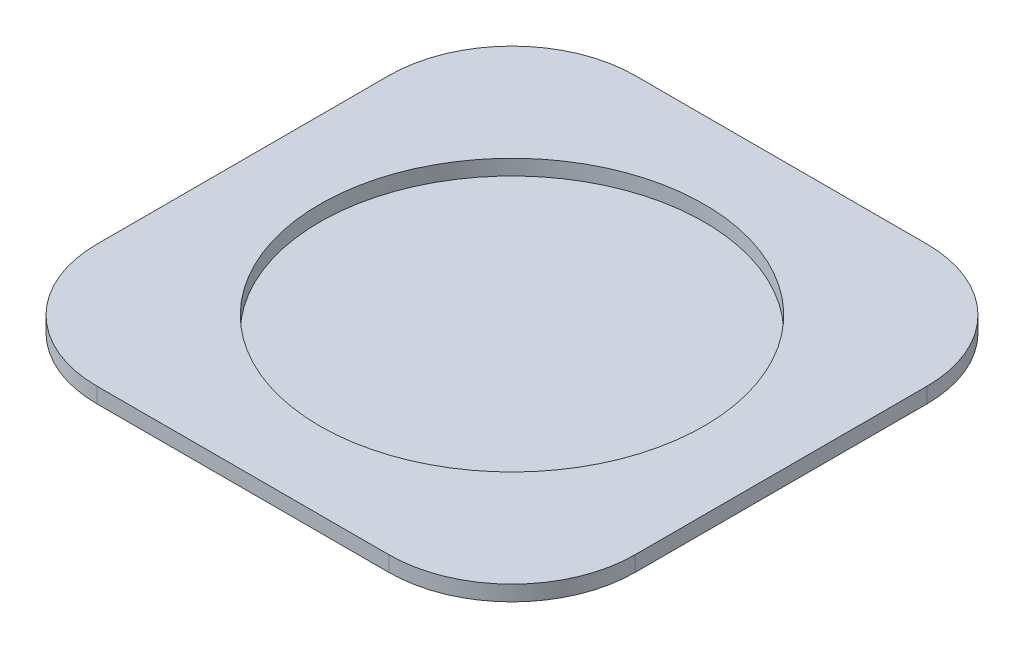
SolidWorks part; units mm, degrees
ref_plane "Front Plane" through (0, 0, 0) normal (0, 0, 1) x (1, 0, 0)
ref_plane "Top Plane" through (0, 0, 0) normal (0, 1, 0) x (1, 0, 0)
ref_plane "Right Plane" through (0, 0, 0) normal (1, 0, 0) x (0, 0, -1)
sketch "Sketch1" plane through (0, 0, 0) normal (0, 1, 0) x (1, 0, 0)
  line L1 (-35, 35) -> (35, 35)
  line L2 (-35, 35) -> (-35, -35)
  line L3 (-35, -35) -> (35, -35)
  line L4 (35, 35) -> (35, -35)
  line L5 (-35, 35) -> (35, -35) construction
  line L6 (-35, -35) -> (35, 35) construction
  circle A0 centre (0, 0) radius 25
  point P0 (0, 0)
  dimension "D3" = 50
  dimension "D1" = 70
  dimension "D2" = 70
extrude "Boss-Extrude1" add sketch "Sketch1" along normal blind 2
fillet "Fillet1" radius 16 4 edges at (35, 1, -35) (-35, 1, 35) (35, 1, 35) (-35, 1, -35)
sketch "Sketch2" plane through (0, 0, 0) normal (0, -1, 0) x (1, 0, 0)
  circle A0 centre (0, 0) radius 32.5
  dimension "D1" = 65
extrude "Boss-Extrude2" add sketch "Sketch2" along normal blind 2
